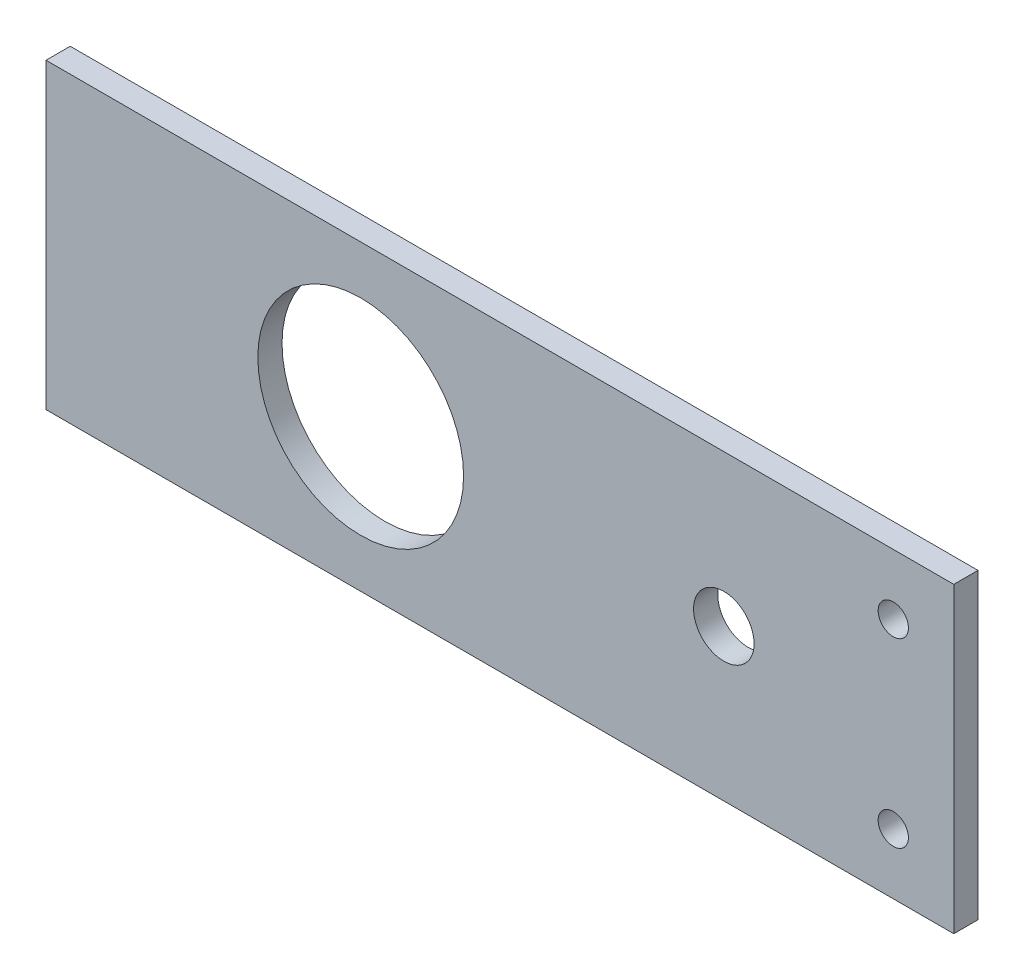
SolidWorks part; units mm, degrees
ref_plane "Front Plane" through (0, 0, 0) normal (0, 0, 1) x (1, 0, 0)
ref_plane "Top Plane" through (0, 0, 0) normal (0, 1, 0) x (1, 0, 0)
ref_plane "Right Plane" through (0, 0, 0) normal (1, 0, 0) x (0, 0, -1)
sketch "Sketch1" plane through (0, 0, 0) normal (0, 0, 1) x (1, 0, 0)
  line L1 (75, -25) -> (-75, -25)
  line L2 (75, -25) -> (75, 25)
  line L3 (75, 25) -> (-75, 25)
  line L4 (-75, -25) -> (-75, 25)
  line L5 (75, -25) -> (-75, 25) construction
  line L6 (75, 25) -> (-75, -25) construction
  circle A1 centre (37, 0) radius 5
  circle A2 centre (-23, 0) radius 17
  point P0 (0, 0)
  dimension "D3" = 60
  dimension "D5" = 34
  dimension "D6" = 10
  dimension "D1" = 150
  dimension "D2" = 50
  dimension "D4" = 38
extrude "Boss-Extrude2" add sketch "Sketch1" along normal blind 4
sketch "Sketch3" plane through (0, 0, 4) normal (0, 0, 1) x (1, 0, 0)
  line L0 (75, -25) -> (75, 25) construction
  line L2 (75, 25) -> (-75, 25) construction
  circle A0 centre (65, 15) radius 2.5
  circle A1 centre (65, -15) radius 2.5
  point P6 (0, 0)
  point P7 (0, 0)
  point P8 (0, 0)
  point P11 (68.2255, 15.5784)
  dimension "D2" = 5
  dimension "D1" = 10
  dimension "D3" = 30
  dimension "D4" = 10
extrude "Cut-Extrude1" cut sketch "Sketch3" against normal blind 10
